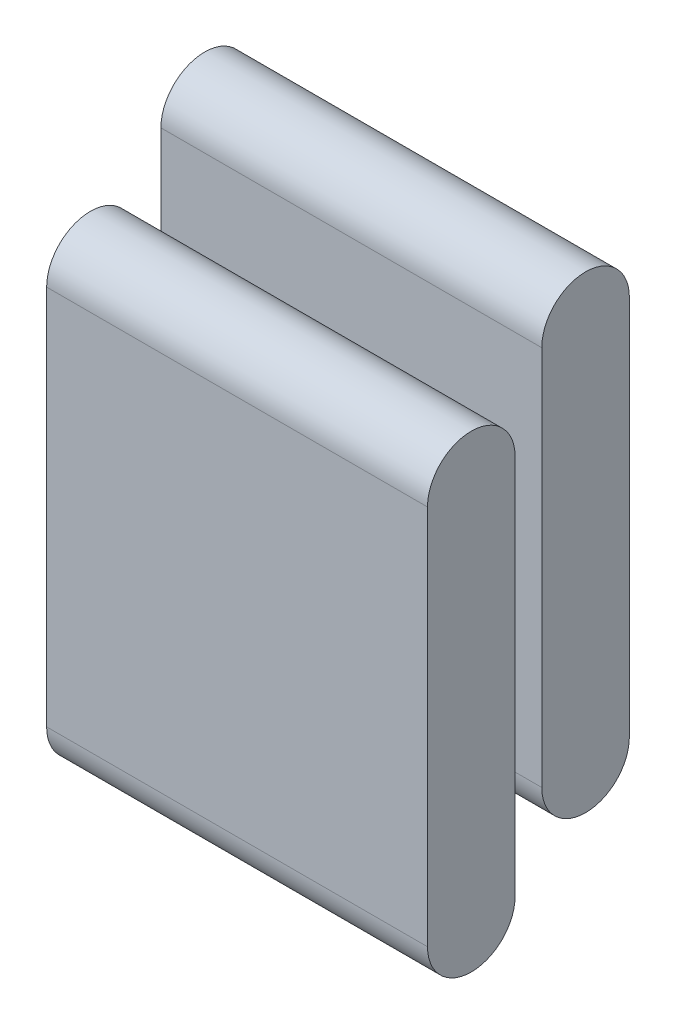
SolidWorks part; units mm, degrees
ref_plane "前视基准面" through (0, 0, 0) normal (0, 0, 1) x (1, 0, 0)
ref_plane "上视基准面" through (0, 0, 0) normal (0, 1, 0) x (1, 0, 0)
ref_plane "右视基准面" through (0, 0, 0) normal (1, 0, 0) x (0, 0, -1)
sketch "草图1" plane through (0, 0, 0) normal (1, 0, 0) x (0, 0, -1)
  line L0 (-10, 16.8205) -> (-10, 6.8205) construction
  line L1 (-6, 11.5) -> (6, 11.5) construction
  line L2 (-6, 11.5) -> (-6, -11.5) construction
  line L3 (-6, -11.5) -> (6, -11.5) construction
  line L4 (6, 11.5) -> (6, -11.5) construction
  line L5 (-6, 11.5) -> (6, -11.5) construction
  line L6 (-6, -11.5) -> (6, 11.5) construction
  line L7 (-8.85, 16.8205) -> (-8.85, 6.8205)
  line L8 (-11.15, 16.8205) -> (-11.15, 6.8205)
  line L9 (0, -5.5) -> (-10, 11.8205) construction
  line L10 (-0.7653, 0) -> (-50000.7653, 0) construction
  line L11 (-13, 14.6987) -> (-13, 4.6987) construction
  line L12 (-11.85, 14.6987) -> (-11.85, 4.6987)
  line L13 (-14.15, 14.6987) -> (-14.15, 4.6987)
  line L14 (0, -5.5) -> (-13, 9.6987) construction
  line L15 (-13, 9.6987) -> (-50013, 9.6987) construction
  line L16 (-10, 11.8205) -> (-50010, 11.8205) construction
  arc A0 (-8.85, 16.8205) -> (-11.15, 16.8205) centre (-10, 16.8205) ccw
  arc A1 (-11.15, 6.8205) -> (-8.85, 6.8205) centre (-10, 6.8205) ccw
  circle A2 centre (0, -5.5) radius 6 construction
  arc A3 (-11.85, 14.6987) -> (-14.15, 14.6987) centre (-13, 14.6987) ccw
  arc A4 (-14.15, 4.6987) -> (-11.85, 4.6987) centre (-13, 4.6987) ccw
  point P0 (0, 0)
  point P8 (-10, 11.8205)
  point P24 (-13, 9.6987)
  dimension "D3" = 1.15
  dimension "D1" = 12
  dimension "D2" = 23
  dimension "D4" = 10
  dimension "D5" = 20
  dimension "D6" = 60
  dimension "D7" = 3
extrude "凸台-拉伸1" add sketch "草图1" along normal blind 10
